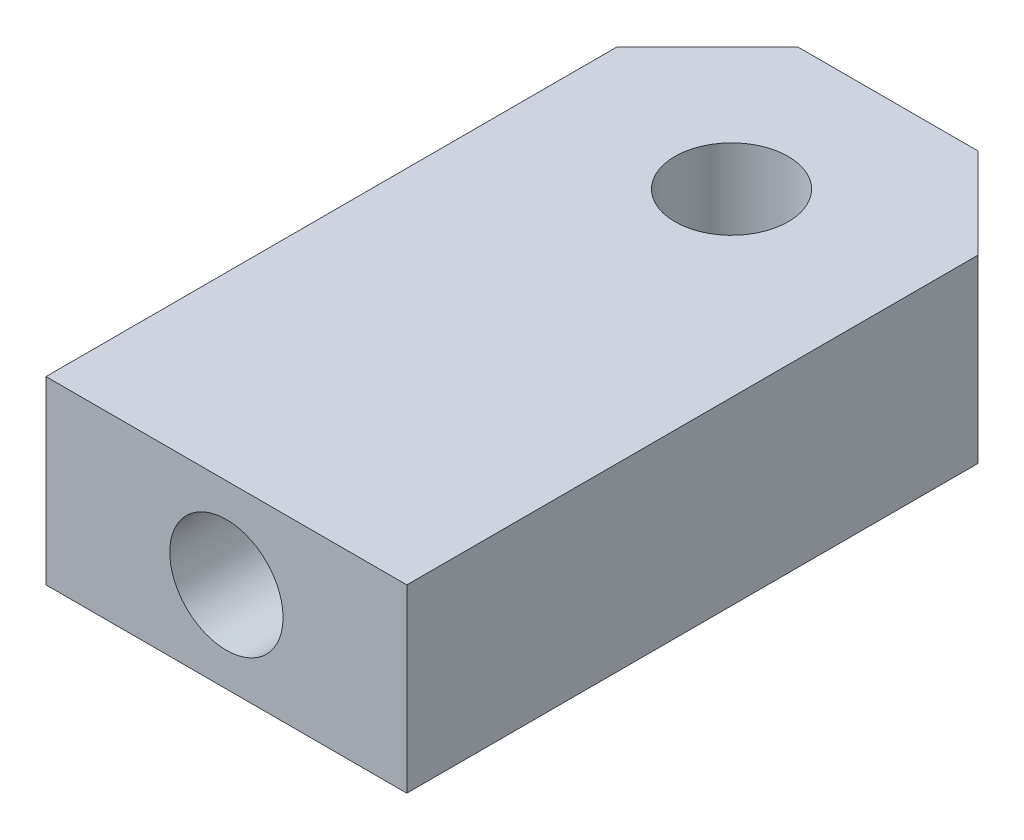
SolidWorks part; units mm, degrees
ref_plane "Front Plane" through (0, 0, 0) normal (0, 0, 1) x (1, 0, 0)
ref_plane "Top Plane" through (0, 0, 0) normal (0, 1, 0) x (1, 0, 0)
ref_plane "Right Plane" through (0, 0, 0) normal (1, 0, 0) x (0, 0, -1)
sketch "Sketch1" plane through (0, 0, 0) normal (0, 1, 0) x (1, 0, 0)
  line L0 (-5, 0) -> (-5, -14)
  line L1 (-5, -14) -> (5, -14)
  line L2 (5, -14) -> (5, 0)
  line L4 (-1.5, -6) -> (1.5, -6) construction
  line L5 (-1.5, -6) -> (-1.5, -22) construction
  line L6 (-1.5, -22) -> (1.5, -22) construction
  line L7 (1.5, -6) -> (1.5, -22) construction
  line L8 (-1.5, -6) -> (1.5, -22) construction
  line L9 (-1.5, -22) -> (1.5, -6) construction
  circle A0 centre (0, 0) radius 1.57
  arc A1 (-5, 0) -> (5, 0) centre (0, 0) cw
  point P5 (0, -14)
  dimension "D1" = 14
  dimension "D2" = 3
  dimension "D3" = 6
  dimension "D4" = 8
  dimension "D5" = 10
sketch "Sketch2" plane through (0, 0, 0) normal (0, 1, 0) x (1, 0, 0)
  line L0 (-5, 0) -> (-5, -14) construction
  line L1 (-5, -14) -> (5, -14) construction
  line L2 (5, -14) -> (5, 0) construction
  line L3 (-5, 0) -> (-5, -14)
  line L4 (-5, -14) -> (5, -14)
  line L5 (5, -14) -> (5, 0)
  line L6 (0, 0) -> (-2.5, 4.3301) construction
  line L7 (-1.5, -6) -> (-1.5, -22) construction
  line L8 (-5, 1.8301) -> (-2.5, 4.3301)
  line L9 (0, 0) -> (2.5, 4.3301) construction
  line L10 (-2.5, 4.3301) -> (2.5, 4.3301)
  line L11 (-5, 1.8301) -> (-5, 0)
  line L12 (2.5, 4.3301) -> (5, 1.8301)
  line L13 (5, 0) -> (5, 1.8301)
  arc A0 (5, 0) -> (-5, 0) centre (0, 0) ccw construction
  circle A1 centre (0, 0) radius 1.57 construction
  arc A2 (5, 0) -> (-5, 0) centre (0, 0) ccw construction
  circle A3 centre (0, 0) radius 1.57
  dimension "D1" = 150
  dimension "D2" = 135
  dimension "D3" = 135
extrude "Boss-Extrude1" add sketch "Sketch2" along normal blind 5
sketch "Sketch3" plane through (0, 0, 14) normal (0, 0, 1) x (1, 0, 0)
  line L0 (-1.5, 0) -> (1.5, 0) construction
  circle A0 centre (0, 2.5) radius 1.57
  dimension "D1" = 2.5
extrude "Cut-Extrude1" cut sketch "Sketch3" against normal blind 8
